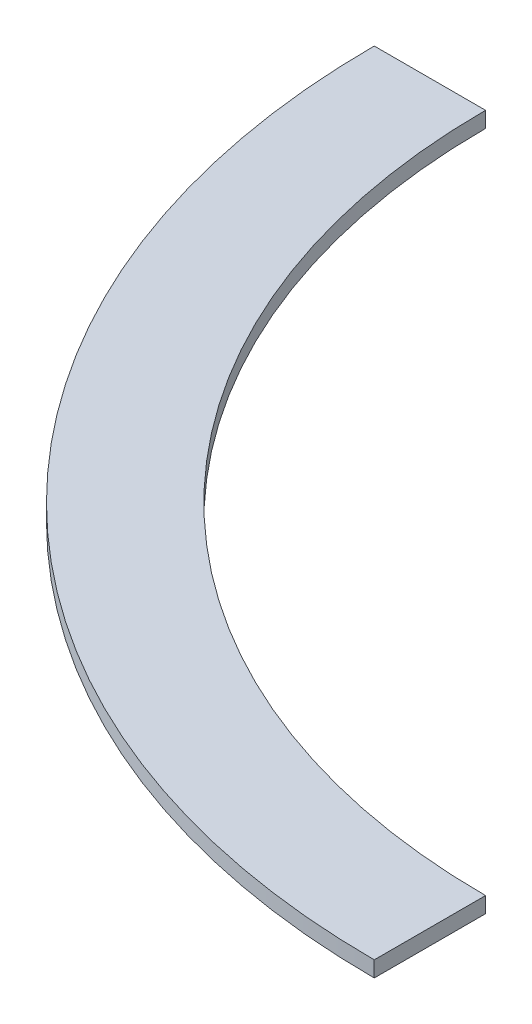
SolidWorks part; units mm, degrees
ref_plane "Front Plane" through (0, 0, 0) normal (0, 0, 1) x (1, 0, 0)
ref_plane "Top Plane" through (0, 0, 0) normal (0, 1, 0) x (1, 0, 0)
ref_plane "Right Plane" through (0, 0, 0) normal (1, 0, 0) x (0, 0, -1)
sketch "Sketch1" plane through (0, 0, 0) normal (0, 1, 0) x (1, 0, 0)
  line L0 (0, -342.9635) -> (0, -399.0975)
  line L1 (-342.9635, 0) -> (-399.0975, 0)
  line L2 (0, 342.9635) -> (0, 399.0975)
  line L3 (342.9635, 0) -> (399.0975, 0)
  circle A0 centre (0, 0) radius 399.0975
  circle A1 centre (0, 0) radius 342.9635
  point P4 (0, 0)
  point P6 (0, 0)
  point P8 (0, 0)
  point P11 (0, 0)
  point P16 (0, 0)
  point P17 (0, 0)
  dimension "D1" = 685.927
  dimension "D2" = 798.195
  dimension "D3" = 4
extrude "Boss-Extrude1" add sketch "Sketch1" along normal blind 7.9375 contours A1 L1 A0 L0
